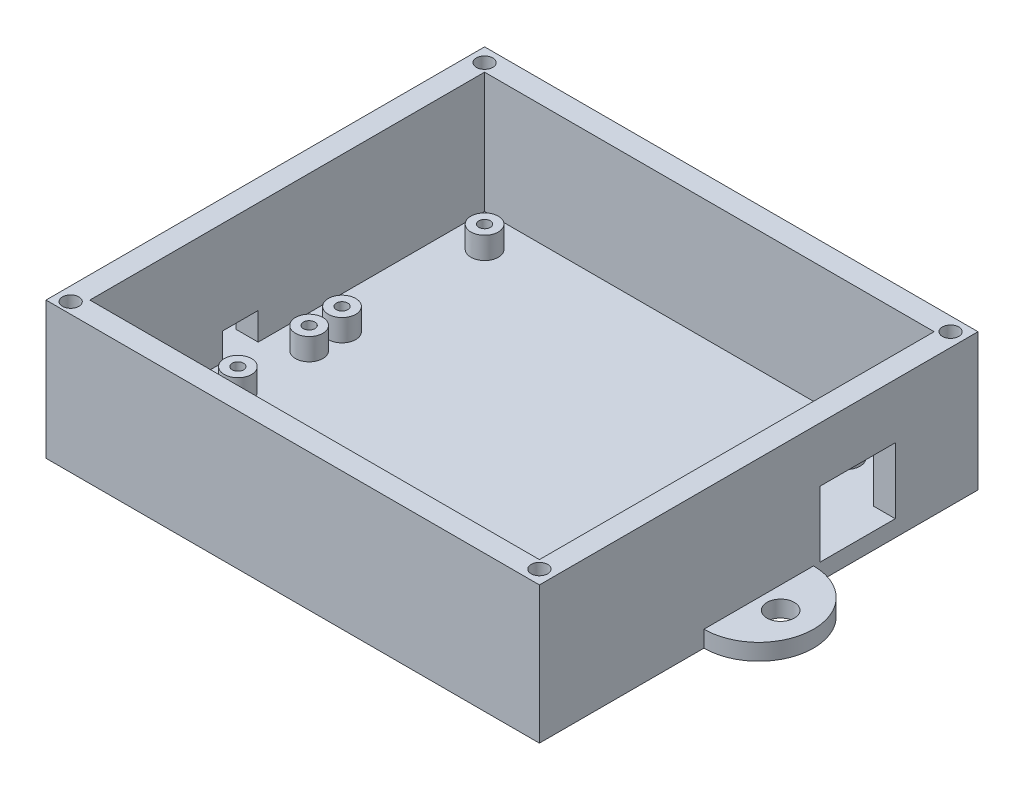
SolidWorks part; units mm, degrees
ref_plane "Front Plane" through (0, 0, 0) normal (0, 0, 1) x (1, 0, 0)
ref_plane "Top Plane" through (0, 0, 0) normal (0, 1, 0) x (1, 0, 0)
ref_plane "Right Plane" through (0, 0, 0) normal (1, 0, 0) x (0, 0, -1)
sketch "Sketch1" plane through (0, 0, 0) normal (0, 1, 0) x (1, 0, 0)
  line L0 (-45, 40) -> (-10, 40)
  line L5 (-45, 40) -> (45, -40) construction
  line L6 (-45, -40) -> (45, 40) construction
  line L7 (10, 40) -> (45, 40)
  line L8 (45, -40) -> (10, -40)
  line L9 (-10, -40) -> (-45, -40)
  line L10 (-10, 40) -> (10, 40)
  line L11 (-10, -40) -> (10, -40)
  line L12 (-45, 40) -> (-45, 10)
  line L13 (-45, -10) -> (-45, -40)
  line L14 (45, 40) -> (45, 10)
  line L15 (45, -10) -> (45, -40)
  arc A5 (-45, -10) -> (-45, 10) centre (-45, 0) cw
  arc A6 (45, -10) -> (45, 10) centre (45, 0) ccw
  circle A7 centre (-49, 0) radius 2.4955
  circle A8 centre (49, 0) radius 2.4955
  point P0 (0, 0)
  dimension "D3" = 10
  dimension "D4" = 4
  dimension "D5" = 4
  dimension "D1" = 90
  dimension "D2" = 80
extrude "Boss-Extrude1" add sketch "Sketch1" along normal blind 3
sketch "Sketch2" plane through (0, 3, 0) normal (0, 1, 0) x (1, 0, 0)
  line L1 (-45, 40) -> (-45, -40) construction
  line L2 (45, 40) -> (-45, 40) construction
  circle A0 centre (-35, 30) radius 2.5
  circle A1 centre (31, 30) radius 2.5
  circle A2 centre (31, 4) radius 2.5
  circle A3 centre (-35, 4) radius 2.5
  circle A4 centre (-35, -2) radius 2.5
  circle A5 centre (31, -2) radius 2.5
  circle A6 centre (-35, -15) radius 2.5
  circle A7 centre (31, -15) radius 2.5
  dimension "D1" = 5
  dimension "D2" = 10
  dimension "D3" = 10
  dimension "D4" = 66
  dimension "D5" = 6
  dimension "D6" = 26
  dimension "D7" = 13
extrude "Boss-Extrude2" add sketch "Sketch2" along normal blind 4
sketch "Sketch3" plane through (0, 3, 0) normal (0, 1, 0) x (1, 0, 0)
  circle A0 centre (-22.5, -25.6742) radius 1.5
  circle A1 centre (22.5, -25.6742) radius 1.5
  dimension "D3" = 3
  dimension "D1" = 22.5
  dimension "D2" = 45
extrude "Cut-Extrude1" cut sketch "Sketch3" against normal blind 3
sketch "Sketch4" plane through (0, 7, 0) normal (0, 1, 0) x (1, 0, 0)
  circle A0 centre (-35, 30) radius 1.05
  circle A1 centre (31, 30) radius 1.05
  circle A2 centre (31, 4) radius 1.05
  circle A3 centre (31, -2) radius 1.05
  circle A4 centre (-35, 4) radius 1.05
  circle A5 centre (-35, -2) radius 1.05
  circle A6 centre (-35, -15) radius 1.05
  circle A7 centre (31, -15) radius 1.05
  dimension "D1" = 2.1
extrude "Cut-Extrude2" cut sketch "Sketch4" against normal blind 4.5
sketch "Sketch6" plane through (0, 3, 0) normal (0, 1, 0) x (1, 0, 0)
  line L1 (-45, 40) -> (45, 40)
  line L2 (-45, 40) -> (-45, -40)
  line L3 (-45, -40) -> (45, -40)
  line L4 (45, 40) -> (45, -40)
  line L5 (-41, 36) -> (41, 36)
  line L6 (-41, 36) -> (-41, -36)
  line L7 (-41, -36) -> (41, -36)
  line L8 (41, 36) -> (41, -36)
  dimension "D1" = 4
  dimension "D2" = 4
  dimension "D3" = 4
  dimension "D4" = 4
extrude "Boss-Extrude3" add sketch "Sketch6" along normal blind 22
sketch "Sketch7" plane through (41, 0, 0) normal (-1, 0, 0) x (0, 0, 1)
  line L0 (36, 3) -> (-36, 3) construction
  line L1 (-24.9136, 3) -> (-11.1636, 3)
  line L2 (-24.9136, 3) -> (-24.9136, 15)
  line L3 (-24.9136, 15) -> (-11.1636, 15)
  line L4 (-11.1636, 3) -> (-11.1636, 15)
  dimension "D1" = 12
  dimension "D2" = 13.75
extrude "Cut-Extrude3" cut sketch "Sketch7" against normal blind 20
sketch "Sketch8" plane through (0, 25, 0) normal (0, 1, 0) x (1, 0, 0)
  line L0 (-45, 40) -> (-45, -40) construction
  line L1 (45, 40) -> (-45, 40) construction
  line L2 (45, -40) -> (45, 40) construction
  line L3 (-45, -40) -> (45, -40) construction
  circle A0 centre (-42.5, 37.5) radius 1.5
  circle A1 centre (42.5, 37.5) radius 1.5
  circle A2 centre (-42.5, -38) radius 1.5
  circle A3 centre (42.5, -37.5) radius 1.5
  dimension "D1" = 3
  dimension "D6" = 2.5
  dimension "D2" = 2.5
  dimension "D3" = 2.5
  dimension "D4" = 2.5
  dimension "D5" = 2
  dimension "D7" = 2.5
  dimension "D8" = 2.5
  dimension "D9" = 2.5
extrude "Cut-Extrude4" cut sketch "Sketch8" against normal blind 10
sketch "Sketch10" plane through (-41, 0, 0) normal (1, 0, 0) x (0, 0, -1)
  line L0 (36, 3) -> (-36, 3) construction
  line L1 (-5.3, 3) -> (-11.8, 3)
  line L2 (-5.3, 3) -> (-5.3, 8.0055)
  line L3 (-5.3, 8.0055) -> (-11.8, 8.0055)
  line L4 (-11.8, 3) -> (-11.8, 8.0055)
  dimension "D1" = 6.5
  dimension "D2" = 2.25
extrude "Cut-Extrude5" cut sketch "Sketch10" against normal blind 10
